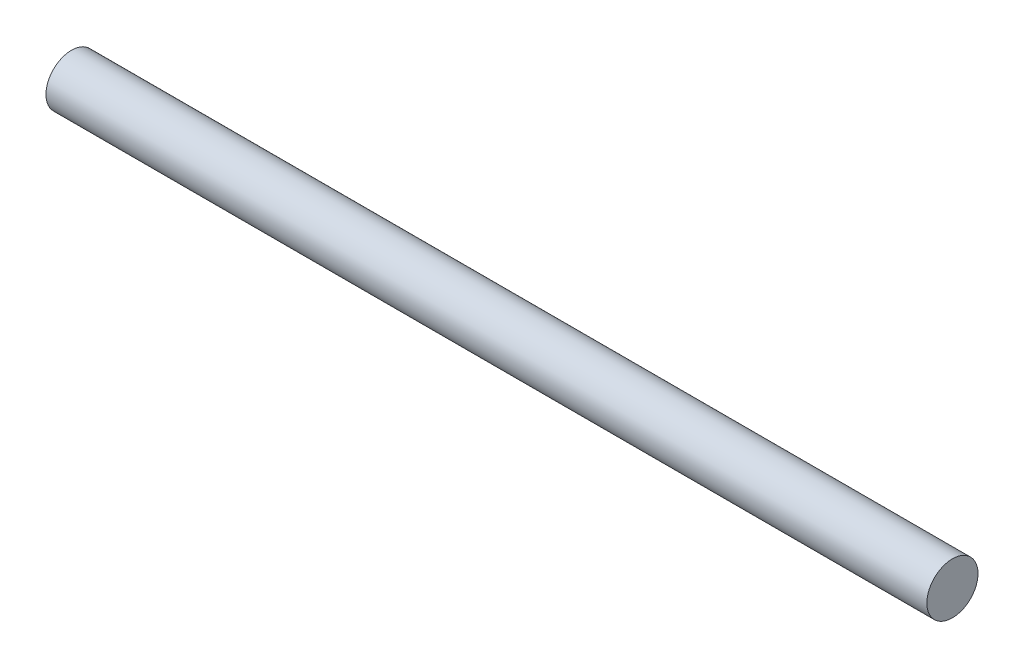
SolidWorks part; units mm, degrees
ref_plane "Plan de face" through (0, 0, 0) normal (0, 0, 1) x (1, 0, 0)
ref_plane "Plan de dessus" through (0, 0, 0) normal (0, 1, 0) x (1, 0, 0)
ref_plane "Plan de droite" through (0, 0, 0) normal (1, 0, 0) x (0, 0, -1)
sketch "Esquisse5" plane through (0, 0, 0) normal (1, 0, 0) x (0, 0, -1)
  circle A0 centre (0, 0) radius 18
extrude "Boss.-Extru.3" add sketch "Esquisse5" along normal blind 620
ref_plane "Plan2" through (10, 0, 0) normal (-1, 0, 0) x (0, 0, 1)
ref_plane "Plan4" through (610, 0, 0) normal (-1, 0, 0) x (0, 0, 1)
sketch "Esquisse6" plane through (10, 0, 0) normal (-1, 0, 0) x (0, 0, 1)
  circle A0 centre (0, 0) radius 18
sketch "Esquisse7" plane through (610, 0, 0) normal (-1, 0, 0) x (0, 0, 1)
  circle A0 centre (0, 0) radius 18
ref_plane "Plan31" through (410, 0, 0) normal (-1, 0, 0) x (0, 0, 1)
sketch "Esquisse32" plane through (410, 0, 0) normal (-1, 0, 0) x (0, 0, 1)
  circle A0 centre (0, 0) radius 18
ref_plane "Plan32" through (210, 0, 0) normal (-1, 0, 0) x (0, 0, 1)
sketch "Esquisse38" plane through (210, 0, 0) normal (-1, 0, 0) x (0, 0, 1)
  circle A0 centre (0, 0) radius 18
